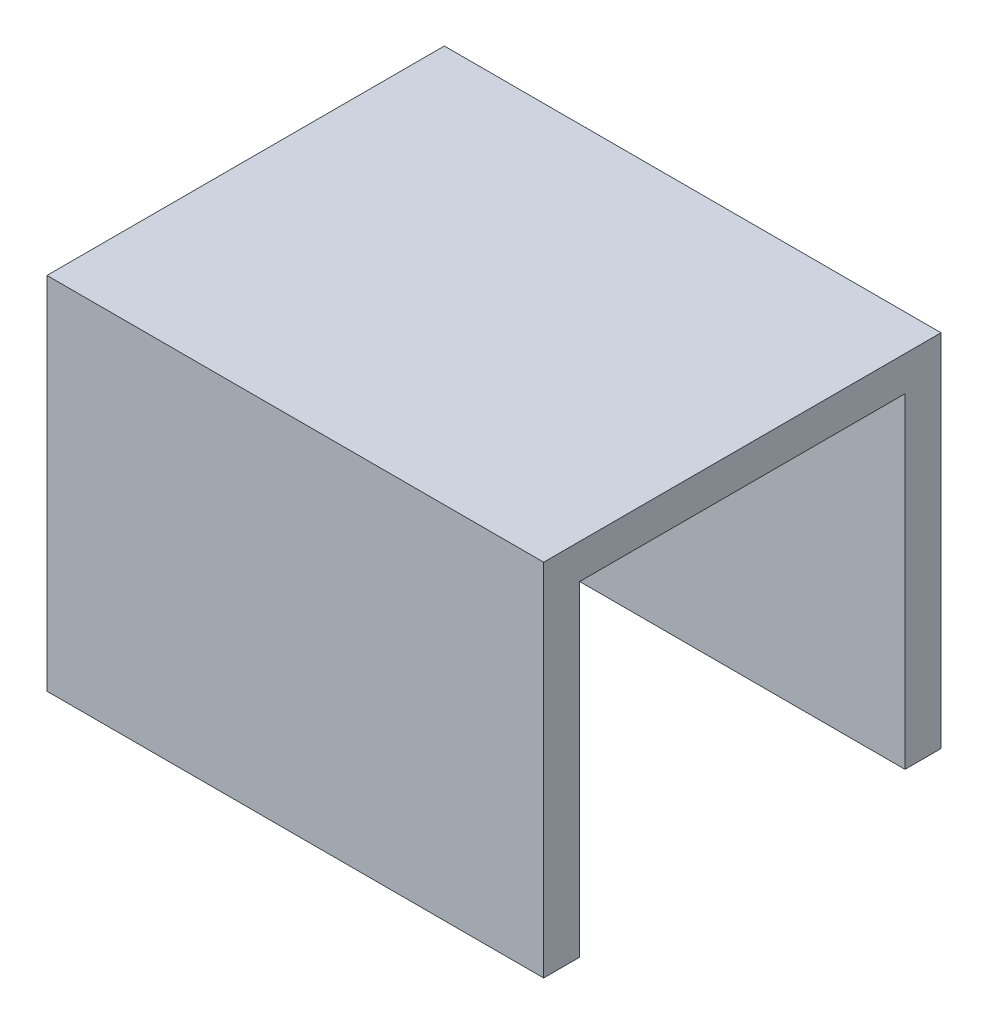
SolidWorks part; units mm, degrees
ref_plane "Front Plane" through (0, 0, 0) normal (0, 0, 1) x (1, 0, 0)
ref_plane "Top Plane" through (0, 0, 0) normal (0, 1, 0) x (1, 0, 0)
ref_plane "Right Plane" through (0, 0, 0) normal (1, 0, 0) x (0, 0, -1)
sketch "Sketch1" plane through (0, 0, 0) normal (0, 1, 0) x (1, 0, 0)
  line L1 (10, -8) -> (-10, -8)
  line L2 (10, -8) -> (10, 8)
  line L3 (10, 8) -> (-10, 8)
  line L4 (-10, -8) -> (-10, 8)
  line L5 (10, -8) -> (-10, 8) construction
  line L6 (10, 8) -> (-10, -8) construction
  point P0 (0, 0)
  dimension "D1" = 16
  dimension "D2" = 20
extrude "Boss-Extrude1" add sketch "Sketch1" along normal blind 14.5
sketch "Sketch2" plane through (-10, 0, 0) normal (-1, 0, 0) x (0, 0, 1)
  line L0 (-8, 0) -> (8, 0) construction
  line L1 (-6.55, 0) -> (6.55, 0)
  line L2 (-6.55, 0) -> (-6.55, 13.1)
  line L3 (-6.55, 13.1) -> (6.55, 13.1)
  line L4 (6.55, 0) -> (6.55, 13.1)
  line L5 (-6.55, 0) -> (-8, 0) construction
  line L6 (6.55, 0) -> (8, 0) construction
  line L7 (-8, 0) -> (8, 0) construction
  line L8 (0, 14.5) -> (0, 13.1) construction
  line L9 (-8, 14.5) -> (8, 14.5) construction
  dimension "D1" = 13.1
extrude "Cut-Extrude1" cut sketch "Sketch2" against normal up to next
